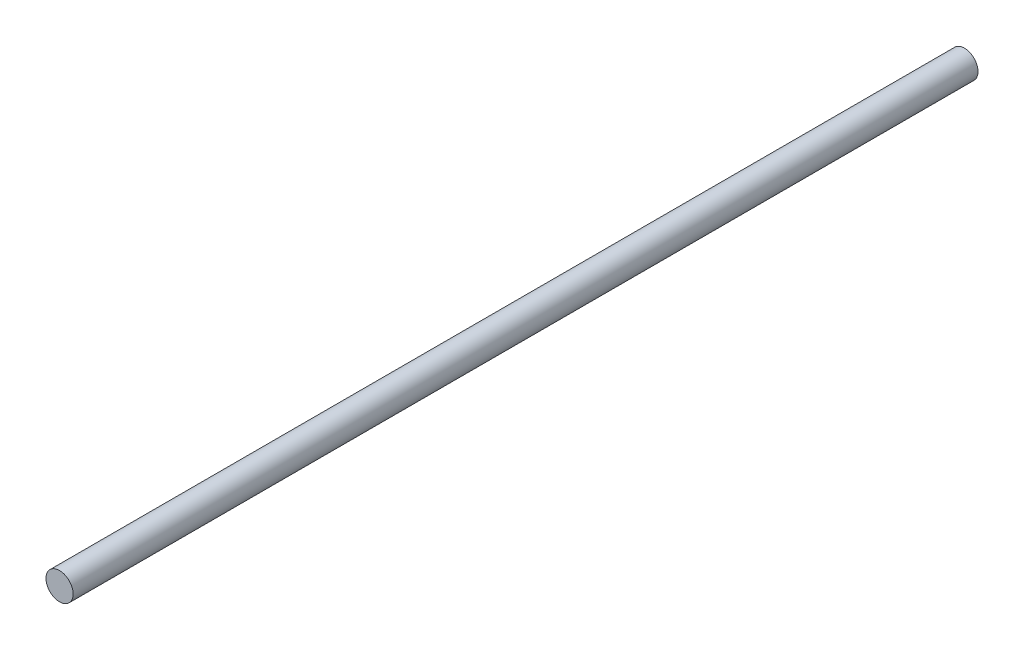
SolidWorks part; units mm, degrees
ref_plane "Front Plane" through (0, 0, 0) normal (0, 0, 1) x (1, 0, 0)
ref_plane "Top Plane" through (0, 0, 0) normal (0, 1, 0) x (1, 0, 0)
ref_plane "Right Plane" through (0, 0, 0) normal (1, 0, 0) x (0, 0, -1)
sketch "Sketch1" plane through (0, 0, 0) normal (0, 0, 1) x (1, 0, 0)
  circle A0 centre (0, 0) radius 3
  dimension "D1" = 6
extrude "Boss-Extrude1" add sketch "Sketch1" along normal mid plane 200
